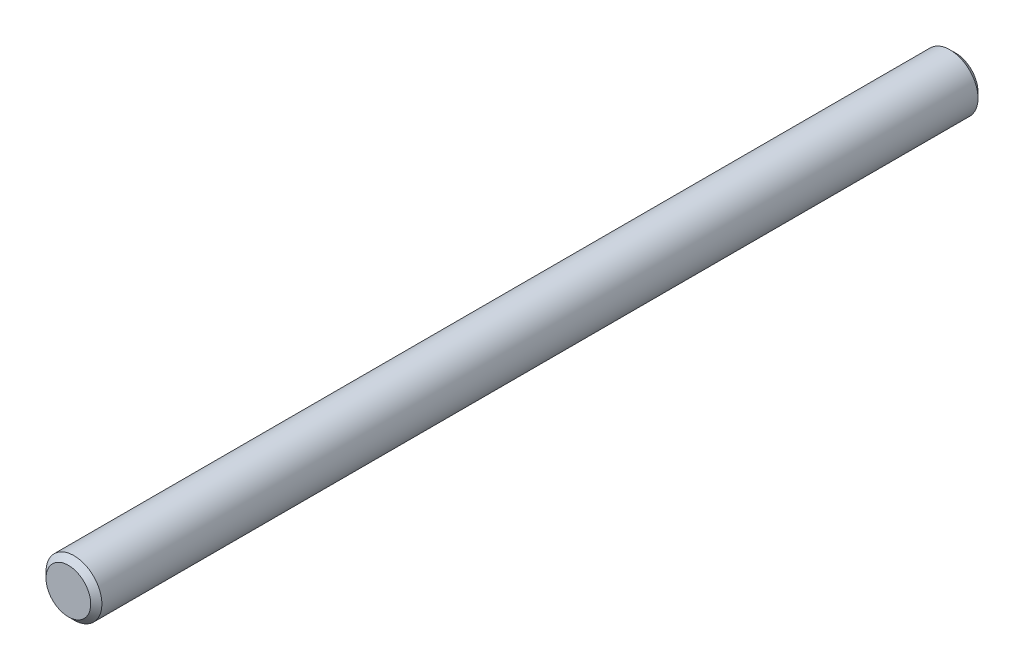
SolidWorks part; units mm, degrees
ref_plane "Front" through (0, 0, 0) normal (0, 0, 1) x (1, 0, 0)
ref_plane "Top" through (0, 0, 0) normal (0, 1, 0) x (1, 0, 0)
ref_plane "Right" through (0, 0, 0) normal (1, 0, 0) x (0, 0, -1)
sketch "Sketch1" plane through (0, 0, 0) normal (0, 0, 1) x (1, 0, 0)
  circle A0 centre (0, 0) radius 4.7625
  dimension "dia" = 9.525
extrude "Extrude1" add sketch "Sketch1" along normal mid plane 151.2
sketch "Sketch2" plane through (0, 0, 0) normal (1, 0, 0) x (0, 0, -1)
  line L0 (-75.6, 4.7625) -> (-70.6, 4.7625) construction
  line L1 (75.6, 4.7625) -> (-75.6, 4.7625) construction
  line L2 (-70.6, 4.7625) -> (-70.6, -4.7625) construction
  line L3 (-75.6, -4.7625) -> (75.6, -4.7625) construction
  point P0 (-75.6, 4.7625)
  point P1 (75.6, 4.7625)
  dimension "D1" = 5
chamfer "Chamfer1" distance 0.9525 angle 45 2 edges at (4.7625, 0, -75.6) (4.7625, 0, 75.6)
equation "\"D1@Chamfer1\" = \"dia@Sketch1\" * .1"
